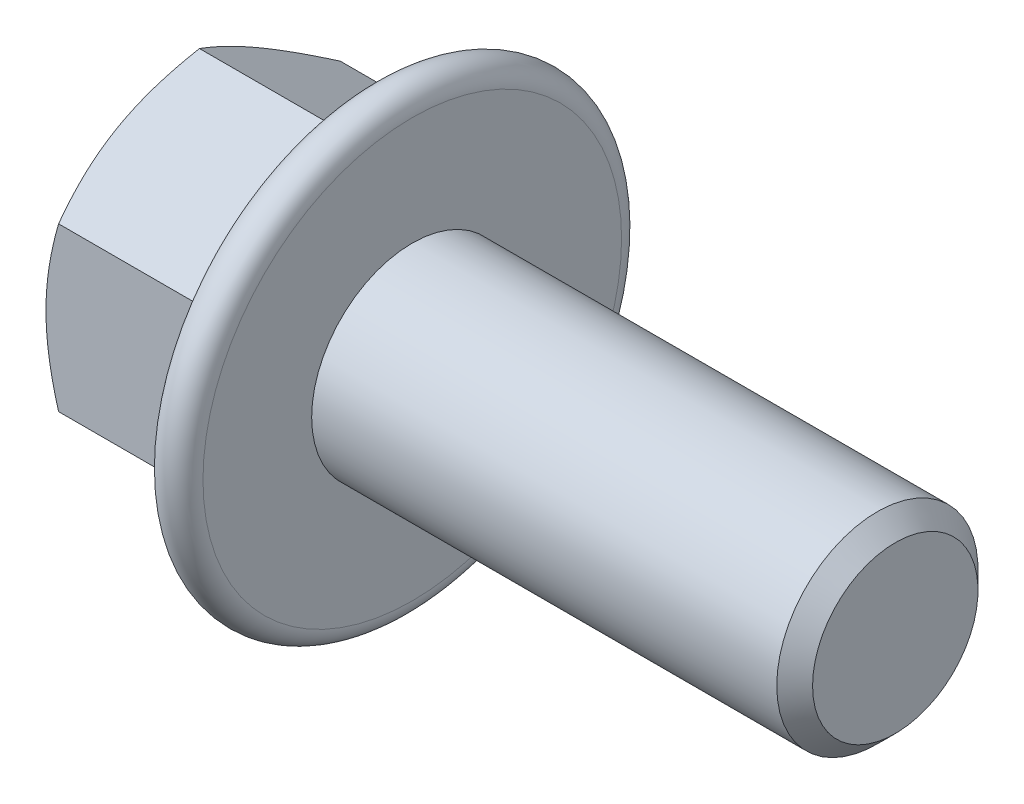
SolidWorks part; units mm, degrees
extrude "BaseHead" add sketch "Sketch1" along normal blind 5.6
sketch "Sketch1" plane through (0, 0, 0) normal (1, 0, 0) x (0, 0, -1)
  line L0 (3.5, 2.0207) -> (3.5, -2.0207)
  line L1 (-3.5, 2.0207) -> (-3.5, -2.0207)
  line L2 (3.5, -2.0207) -> (0, -4.0415)
  line L3 (0, -4.0415) -> (-3.5, -2.0207)
  line L4 (3.5, 2.0207) -> (0, 4.0415)
  line L5 (0, 4.0415) -> (-3.5, 2.0207)
  dimension "Width_flats" = 7
  dimension "D2" = 120
  dimension "D3" = 3.5
  dimension "D4" = 3.5
  dimension "D5" = 3.5
ref_plane "Plane1" through (0, 0, 0) normal (0, 0, 1) x (1, 0, 0)
ref_plane "Plane2" through (0, 0, 0) normal (0, 1, 0) x (1, 0, 0)
ref_plane "Plane3" through (0, 0, 0) normal (1, 0, 0) x (0, 0, -1)
sketch "BodySke" plane through (0, 0, 0) normal (0, 0, 1) x (1, 0, 0)
  line L0 (0, 2.0207) -> (0, -2.0207) construction
  line L1 (0, 0) -> (17.6, 0)
  line L2 (0, 0) -> (0, 2.5)
  line L3 (0, 2.5) -> (17.155, 2.5)
  line L4 (17.6, 0) -> (17.6, 2.055)
  line L5 (5.6, 4.0415) -> (5.6, 2.0207) construction
  line L6 (17.6, 2.055) -> (17.155, 2.5)
  line L7 (0, 0) -> (96.52, 0) construction
  line L8 (17.6, -2.055) -> (17.155, -2.5) construction
  line L9 (0, -2.5) -> (17.155, -2.5) construction
  line L10 (6.4, 15.24) -> (6.4, -1.27) construction
  line L11 (5.6, 15.24) -> (5.6, -1.27) construction
  line L12 (5.6, 2.0207) -> (5.6, -2.0207) construction
  dimension "Diameter" = 5
revolve "BaseBody" add sketch "BodySke"
cosmetic thread "ThreadCosmetic" [suppressed]
fillet "HeadFillet" [suppressed] radius 0.2
sketch "Sketch3" plane through (0, 0, 0) normal (0, 0, 1) x (1, 0, 0)
  line L0 (0, 3.5) -> (3.1994, 9.0415)
  line L1 (0, 4.0415) -> (0, 2.0207) construction
  line L2 (3.1994, 9.0415) -> (3.1994, 14.0415)
  line L3 (3.1994, 14.0415) -> (-10, 14.0415)
  line L4 (-10, 14.0415) -> (-10, 3.5)
  line L5 (-10, 3.5) -> (0, 3.5)
  line L6 (0, 0) -> (99.06, 0) construction
  line L7 (5.6, 4.0415) -> (0, 4.0415) construction
  dimension "D1" = 3.5
  dimension "D2" = 5
  dimension "D3" = 10
  dimension "D4" = 5
  dimension "Head_ch_ang" = 30
revolve "HeadChamfer" cut sketch "Sketch3" angle 360 about L6
sketch "Sketch4" plane through (0, 0, 0) normal (0, 0, 1) x (1, 0, 0)
  line L0 (2.6753, 0) -> (4.6302, 5.371)
  line L1 (5.6, 4.0415) -> (5.6, 2.0207) construction
  line L2 (4.6, 34.3444) -> (4.6, 16.9779) construction
  line L3 (5.6, 0) -> (5.6, 5.2)
  line L4 (8.3021, 5.7) -> (20.1618, 5.7) construction
  line L5 (0, 0) -> (95.25, 0) construction
  line L6 (0, 0) -> (96.52, 0) construction
  line L7 (2.6753, 0) -> (5.6, 0)
  line L8 (8.3021, -5.7) -> (20.1618, -5.7) construction
  arc A0 (5.6, 5.2) -> (4.6302, 5.371) centre (5.1, 5.2) ccw
  dimension "D1" = 20
  dimension "Flange_thickness" = 1
  dimension "Flange_dia" = 11.4
revolve "Flange" add sketch "Sketch4" angle 360 about L5
fillet "FlangeHexFillet" radius 0.1 6 edges
sketch "ThdSchSke" plane through (0, 0, 0) normal (0, 0, 1) x (1, 0, 0)
  line L0 (6.4, -2.055) -> (6.0884, -2.5)
  line L1 (6.4, -2.055) -> (6.7116, -2.5)
  line L2 (6.7116, -2.5) -> (6.7116, -3.125)
  line L3 (-3.175, 0) -> (5.1513, 0) construction
  line L5 (6.7116, -3.125) -> (6.0884, -3.125)
  line L6 (6.0884, -3.125) -> (6.0884, -2.5)
  dimension "Thread_minor" = 4.11
  dimension "Diameter" = 5
  dimension "Start" = 6.4
revolve "ThreadSchematic" [suppressed] cut sketch "ThdSchSke" angle 360 about L3
pattern_linear "ThdSchPat" [suppressed]
equation "\"D3@Sketch1\" = \"Width_flats@Sketch1\" / 2"
equation "\"D4@Sketch1\" = \"D3@Sketch1\""
equation "\"D5@Sketch1\" = \"D4@Sketch1\""
equation "\"Thread_minor@ThreadCosmetic\" = \"Minor_dia@BodySke\""
equation "\"D1@Sketch3\" = \"Width_flats@Sketch1\" / 2"
equation "\"Thread_length@ThreadCosmetic\" = ((sgn( (\"Length@BodySke\" - \"Advance@BodySke\" ) - \"Thread_nom@BodySke\" )-1)*( (\"Length@BodySke\" - \"Advance@BodySke\" ) - \"Thread_nom@BodySke\" ))/-2+ \"Thread_nom@BodySke\""
equation "\"Thread_minor@ThdSchSke\" = \"Minor_dia@BodySke\""
equation "\"Diameter@ThdSchSke\" = \"Diameter@BodySke\""
equation "\"Overcut@ThdSchSke\" = \"Diameter@BodySke\" * 1.25"
equation "\"Start@ThdSchSke\" = \"Head_ht@BaseHead\" + \"Length@BodySke\" - \"Thread_length@ThreadCosmetic\"  '---Non-countersunk---"
equation "\"Num_threads@ThdSchPat\" = int( \"Thread_length@ThreadCosmetic\" / \"Advance@BodySke\" + 0.999 )  + 1"
equation "\"Advance@ThdSchPat\" = \"Thread_length@ThreadCosmetic\" /  (\"Num_threads@ThdSchPat\" - 1) 'relax it"
equation "\"Num_threads@ThdSchPat\" = \"Num_threads@ThdSchPat\" - sgn( \"Num_threads@ThdSchPat\" - 1) '---chamfered tips only---"
